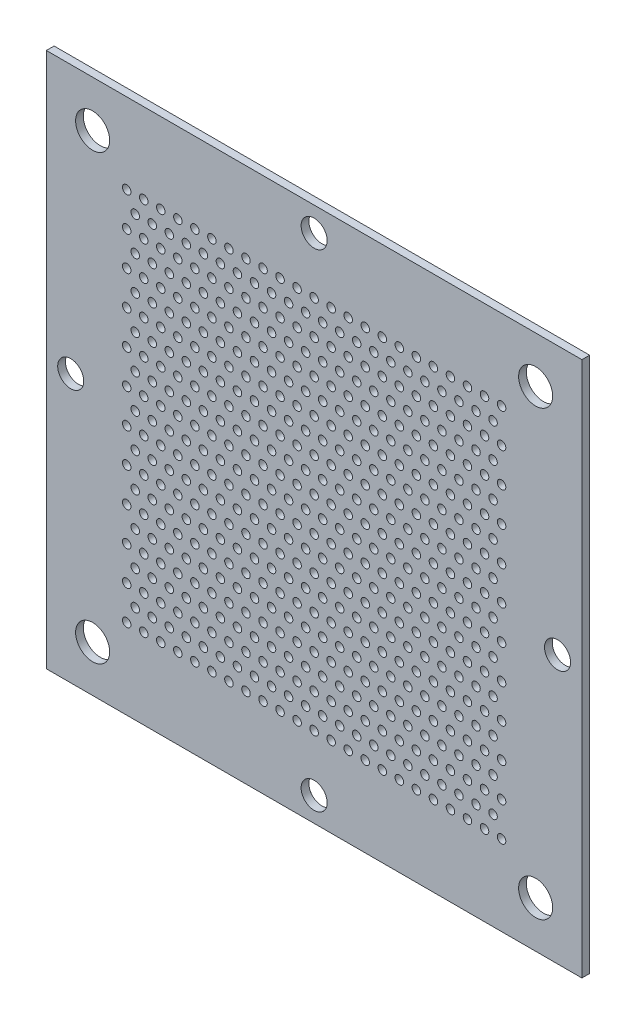
SolidWorks part; units mm, degrees
ref_plane "Front Plane" through (0, 0, 0) normal (0, 0, 1) x (1, 0, 0)
ref_plane "Top Plane" through (0, 0, 0) normal (0, 1, 0) x (1, 0, 0)
ref_plane "Right Plane" through (0, 0, 0) normal (1, 0, 0) x (0, 0, -1)
sketch "Model" plane through (0, 0, 0) normal (0, 0, 1) x (1, 0, 0)
  line L0 (-16.5, -16.5) -> (-16.5, 93.5)
  line L1 (-16.5, 93.5) -> (93.5, 93.5)
  line L2 (93.5, 93.5) -> (93.5, -16.5)
  line L3 (93.5, -16.5) -> (-16.5, -16.5)
  circle A0 centre (84, 84) radius 3.5
  circle A1 centre (-7, 84) radius 3.5
  circle A2 centre (-7, -7) radius 3.5
  circle A3 centre (84, -7) radius 3.5
  circle A4 centre (77, 0) radius 0.875
  circle A5 centre (73.5, 0) radius 0.875
  circle A6 centre (70, 0) radius 0.875
  circle A7 centre (66.5, 0) radius 0.875
  circle A8 centre (63, 0) radius 0.875
  circle A9 centre (59.5, 0) radius 0.875
  circle A10 centre (56, 0) radius 0.875
  circle A11 centre (52.5, 0) radius 0.875
  circle A12 centre (49, 0) radius 0.875
  circle A13 centre (45.5, 0) radius 0.875
  circle A14 centre (42, 0) radius 0.875
  circle A15 centre (38.5, 0) radius 0.875
  circle A16 centre (35, 0) radius 0.875
  circle A17 centre (31.5, 0) radius 0.875
  circle A18 centre (28, 0) radius 0.875
  circle A19 centre (24.5, 0) radius 0.875
  circle A20 centre (21, 0) radius 0.875
  circle A21 centre (17.5, 0) radius 0.875
  circle A22 centre (14, 0) radius 0.875
  circle A23 centre (10.5, 0) radius 0.875
  circle A24 centre (7, 0) radius 0.875
  circle A25 centre (3.5, 0) radius 0.875
  circle A26 centre (0, 0) radius 0.875
  circle A27 centre (75.25, 3.5) radius 0.875
  circle A28 centre (71.75, 3.5) radius 0.875
  circle A29 centre (68.25, 3.5) radius 0.875
  circle A30 centre (64.75, 3.5) radius 0.875
  circle A31 centre (61.25, 3.5) radius 0.875
  circle A32 centre (57.75, 3.5) radius 0.875
  circle A33 centre (54.25, 3.5) radius 0.875
  circle A34 centre (50.75, 3.5) radius 0.875
  circle A35 centre (47.25, 3.5) radius 0.875
  circle A36 centre (43.75, 3.5) radius 0.875
  circle A37 centre (40.25, 3.5) radius 0.875
  circle A38 centre (36.75, 3.5) radius 0.875
  circle A39 centre (33.25, 3.5) radius 0.875
  circle A40 centre (29.75, 3.5) radius 0.875
  circle A41 centre (26.25, 3.5) radius 0.875
  circle A42 centre (22.75, 3.5) radius 0.875
  circle A43 centre (19.25, 3.5) radius 0.875
  circle A44 centre (15.75, 3.5) radius 0.875
  circle A45 centre (12.25, 3.5) radius 0.875
  circle A46 centre (8.75, 3.5) radius 0.875
  circle A47 centre (5.25, 3.5) radius 0.875
  circle A48 centre (1.75, 3.5) radius 0.875
  circle A49 centre (77, 7) radius 0.875
  circle A50 centre (73.5, 7) radius 0.875
  circle A51 centre (70, 7) radius 0.875
  circle A52 centre (66.5, 7) radius 0.875
  circle A53 centre (63, 7) radius 0.875
  circle A54 centre (59.5, 7) radius 0.875
  circle A55 centre (56, 7) radius 0.875
  circle A56 centre (52.5, 7) radius 0.875
  circle A57 centre (49, 7) radius 0.875
  circle A58 centre (45.5, 7) radius 0.875
  circle A59 centre (42, 7) radius 0.875
  circle A60 centre (38.5, 7) radius 0.875
  circle A61 centre (35, 7) radius 0.875
  circle A62 centre (31.5, 7) radius 0.875
  circle A63 centre (28, 7) radius 0.875
  circle A64 centre (24.5, 7) radius 0.875
  circle A65 centre (21, 7) radius 0.875
  circle A66 centre (17.5, 7) radius 0.875
  circle A67 centre (14, 7) radius 0.875
  circle A68 centre (10.5, 7) radius 0.875
  circle A69 centre (7, 7) radius 0.875
  circle A70 centre (3.5, 7) radius 0.875
  circle A71 centre (0, 7) radius 0.875
  circle A72 centre (75.25, 10.5) radius 0.875
  circle A73 centre (71.75, 10.5) radius 0.875
  circle A74 centre (68.25, 10.5) radius 0.875
  circle A75 centre (64.75, 10.5) radius 0.875
  circle A76 centre (61.25, 10.5) radius 0.875
  circle A77 centre (57.75, 10.5) radius 0.875
  circle A78 centre (54.25, 10.5) radius 0.875
  circle A79 centre (50.75, 10.5) radius 0.875
  circle A80 centre (47.25, 10.5) radius 0.875
  circle A81 centre (43.75, 10.5) radius 0.875
  circle A82 centre (40.25, 10.5) radius 0.875
  circle A83 centre (36.75, 10.5) radius 0.875
  circle A84 centre (33.25, 10.5) radius 0.875
  circle A85 centre (29.75, 10.5) radius 0.875
  circle A86 centre (26.25, 10.5) radius 0.875
  circle A87 centre (22.75, 10.5) radius 0.875
  circle A88 centre (19.25, 10.5) radius 0.875
  circle A89 centre (15.75, 10.5) radius 0.875
  circle A90 centre (12.25, 10.5) radius 0.875
  circle A91 centre (8.75, 10.5) radius 0.875
  circle A92 centre (5.25, 10.5) radius 0.875
  circle A93 centre (1.75, 10.5) radius 0.875
  circle A94 centre (77, 14) radius 0.875
  circle A95 centre (73.5, 14) radius 0.875
  circle A96 centre (70, 14) radius 0.875
  circle A97 centre (66.5, 14) radius 0.875
  circle A98 centre (63, 14) radius 0.875
  circle A99 centre (59.5, 14) radius 0.875
  circle A100 centre (56, 14) radius 0.875
  circle A101 centre (52.5, 14) radius 0.875
  circle A102 centre (49, 14) radius 0.875
  circle A103 centre (45.5, 14) radius 0.875
  circle A104 centre (42, 14) radius 0.875
  circle A105 centre (38.5, 14) radius 0.875
  circle A106 centre (35, 14) radius 0.875
  circle A107 centre (31.5, 14) radius 0.875
  circle A108 centre (28, 14) radius 0.875
  circle A109 centre (24.5, 14) radius 0.875
  circle A110 centre (21, 14) radius 0.875
  circle A111 centre (17.5, 14) radius 0.875
  circle A112 centre (14, 14) radius 0.875
  circle A113 centre (10.5, 14) radius 0.875
  circle A114 centre (7, 14) radius 0.875
  circle A115 centre (3.5, 14) radius 0.875
  circle A116 centre (0, 14) radius 0.875
  circle A117 centre (75.25, 17.5) radius 0.875
  circle A118 centre (71.75, 17.5) radius 0.875
  circle A119 centre (68.25, 17.5) radius 0.875
  circle A120 centre (64.75, 17.5) radius 0.875
  circle A121 centre (61.25, 17.5) radius 0.875
  circle A122 centre (57.75, 17.5) radius 0.875
  circle A123 centre (54.25, 17.5) radius 0.875
  circle A124 centre (50.75, 17.5) radius 0.875
  circle A125 centre (47.25, 17.5) radius 0.875
  circle A126 centre (43.75, 17.5) radius 0.875
  circle A127 centre (40.25, 17.5) radius 0.875
  circle A128 centre (36.75, 17.5) radius 0.875
  circle A129 centre (33.25, 17.5) radius 0.875
  circle A130 centre (29.75, 17.5) radius 0.875
  circle A131 centre (26.25, 17.5) radius 0.875
  circle A132 centre (22.75, 17.5) radius 0.875
  circle A133 centre (19.25, 17.5) radius 0.875
  circle A134 centre (15.75, 17.5) radius 0.875
  circle A135 centre (12.25, 17.5) radius 0.875
  circle A136 centre (8.75, 17.5) radius 0.875
  circle A137 centre (5.25, 17.5) radius 0.875
  circle A138 centre (1.75, 17.5) radius 0.875
  circle A139 centre (77, 21) radius 0.875
  circle A140 centre (73.5, 21) radius 0.875
  circle A141 centre (70, 21) radius 0.875
  circle A142 centre (66.5, 21) radius 0.875
  circle A143 centre (63, 21) radius 0.875
  circle A144 centre (59.5, 21) radius 0.875
  circle A145 centre (56, 21) radius 0.875
  circle A146 centre (52.5, 21) radius 0.875
  circle A147 centre (49, 21) radius 0.875
  circle A148 centre (45.5, 21) radius 0.875
  circle A149 centre (42, 21) radius 0.875
  circle A150 centre (38.5, 21) radius 0.875
  circle A151 centre (35, 21) radius 0.875
  circle A152 centre (31.5, 21) radius 0.875
  circle A153 centre (28, 21) radius 0.875
  circle A154 centre (24.5, 21) radius 0.875
  circle A155 centre (21, 21) radius 0.875
  circle A156 centre (17.5, 21) radius 0.875
  circle A157 centre (14, 21) radius 0.875
  circle A158 centre (10.5, 21) radius 0.875
  circle A159 centre (7, 21) radius 0.875
  circle A160 centre (3.5, 21) radius 0.875
  circle A161 centre (0, 21) radius 0.875
  circle A162 centre (75.25, 24.5) radius 0.875
  circle A163 centre (71.75, 24.5) radius 0.875
  circle A164 centre (68.25, 24.5) radius 0.875
  circle A165 centre (64.75, 24.5) radius 0.875
  circle A166 centre (61.25, 24.5) radius 0.875
  circle A167 centre (57.75, 24.5) radius 0.875
  circle A168 centre (54.25, 24.5) radius 0.875
  circle A169 centre (50.75, 24.5) radius 0.875
  circle A170 centre (47.25, 24.5) radius 0.875
  circle A171 centre (43.75, 24.5) radius 0.875
  circle A172 centre (40.25, 24.5) radius 0.875
  circle A173 centre (36.75, 24.5) radius 0.875
  circle A174 centre (33.25, 24.5) radius 0.875
  circle A175 centre (29.75, 24.5) radius 0.875
  circle A176 centre (26.25, 24.5) radius 0.875
  circle A177 centre (22.75, 24.5) radius 0.875
  circle A178 centre (19.25, 24.5) radius 0.875
  circle A179 centre (15.75, 24.5) radius 0.875
  circle A180 centre (12.25, 24.5) radius 0.875
  circle A181 centre (8.75, 24.5) radius 0.875
  circle A182 centre (5.25, 24.5) radius 0.875
  circle A183 centre (1.75, 24.5) radius 0.875
  circle A184 centre (77, 28) radius 0.875
  circle A185 centre (73.5, 28) radius 0.875
  circle A186 centre (70, 28) radius 0.875
  circle A187 centre (66.5, 28) radius 0.875
  circle A188 centre (63, 28) radius 0.875
  circle A189 centre (59.5, 28) radius 0.875
  circle A190 centre (56, 28) radius 0.875
  circle A191 centre (52.5, 28) radius 0.875
  circle A192 centre (49, 28) radius 0.875
  circle A193 centre (45.5, 28) radius 0.875
  circle A194 centre (42, 28) radius 0.875
  circle A195 centre (38.5, 28) radius 0.875
  circle A196 centre (35, 28) radius 0.875
  circle A197 centre (31.5, 28) radius 0.875
  circle A198 centre (28, 28) radius 0.875
  circle A199 centre (24.5, 28) radius 0.875
  circle A200 centre (21, 28) radius 0.875
  circle A201 centre (17.5, 28) radius 0.875
  circle A202 centre (14, 28) radius 0.875
  circle A203 centre (10.5, 28) radius 0.875
  circle A204 centre (7, 28) radius 0.875
  circle A205 centre (3.5, 28) radius 0.875
  circle A206 centre (0, 28) radius 0.875
  circle A207 centre (75.25, 31.5) radius 0.875
  circle A208 centre (71.75, 31.5) radius 0.875
  circle A209 centre (68.25, 31.5) radius 0.875
  circle A210 centre (64.75, 31.5) radius 0.875
  circle A211 centre (61.25, 31.5) radius 0.875
  circle A212 centre (57.75, 31.5) radius 0.875
  circle A213 centre (54.25, 31.5) radius 0.875
  circle A214 centre (50.75, 31.5) radius 0.875
  circle A215 centre (47.25, 31.5) radius 0.875
  circle A216 centre (43.75, 31.5) radius 0.875
  circle A217 centre (40.25, 31.5) radius 0.875
  circle A218 centre (36.75, 31.5) radius 0.875
  circle A219 centre (33.25, 31.5) radius 0.875
  circle A220 centre (29.75, 31.5) radius 0.875
  circle A221 centre (26.25, 31.5) radius 0.875
  circle A222 centre (22.75, 31.5) radius 0.875
  circle A223 centre (19.25, 31.5) radius 0.875
  circle A224 centre (15.75, 31.5) radius 0.875
  circle A225 centre (12.25, 31.5) radius 0.875
  circle A226 centre (8.75, 31.5) radius 0.875
  circle A227 centre (5.25, 31.5) radius 0.875
  circle A228 centre (1.75, 31.5) radius 0.875
  circle A229 centre (77, 35) radius 0.875
  circle A230 centre (73.5, 35) radius 0.875
  circle A231 centre (70, 35) radius 0.875
  circle A232 centre (66.5, 35) radius 0.875
  circle A233 centre (63, 35) radius 0.875
  circle A234 centre (59.5, 35) radius 0.875
  circle A235 centre (56, 35) radius 0.875
  circle A236 centre (52.5, 35) radius 0.875
  circle A237 centre (49, 35) radius 0.875
  circle A238 centre (45.5, 35) radius 0.875
  circle A239 centre (42, 35) radius 0.875
  circle A240 centre (38.5, 35) radius 0.875
  circle A241 centre (35, 35) radius 0.875
  circle A242 centre (31.5, 35) radius 0.875
  circle A243 centre (28, 35) radius 0.875
  circle A244 centre (24.5, 35) radius 0.875
  circle A245 centre (21, 35) radius 0.875
  circle A246 centre (17.5, 35) radius 0.875
  circle A247 centre (14, 35) radius 0.875
  circle A248 centre (10.5, 35) radius 0.875
  circle A249 centre (7, 35) radius 0.875
  circle A250 centre (3.5, 35) radius 0.875
  circle A251 centre (0, 35) radius 0.875
  circle A252 centre (75.25, 38.5) radius 0.875
  circle A253 centre (71.75, 38.5) radius 0.875
  circle A254 centre (68.25, 38.5) radius 0.875
  circle A255 centre (64.75, 38.5) radius 0.875
  circle A256 centre (61.25, 38.5) radius 0.875
  circle A257 centre (57.75, 38.5) radius 0.875
  circle A258 centre (54.25, 38.5) radius 0.875
  circle A259 centre (50.75, 38.5) radius 0.875
  circle A260 centre (47.25, 38.5) radius 0.875
  circle A261 centre (43.75, 38.5) radius 0.875
  circle A262 centre (40.25, 38.5) radius 0.875
  circle A263 centre (36.75, 38.5) radius 0.875
  circle A264 centre (33.25, 38.5) radius 0.875
  circle A265 centre (29.75, 38.5) radius 0.875
  circle A266 centre (26.25, 38.5) radius 0.875
  circle A267 centre (22.75, 38.5) radius 0.875
  circle A268 centre (19.25, 38.5) radius 0.875
  circle A269 centre (15.75, 38.5) radius 0.875
  circle A270 centre (12.25, 38.5) radius 0.875
  circle A271 centre (8.75, 38.5) radius 0.875
  circle A272 centre (5.25, 38.5) radius 0.875
  circle A273 centre (1.75, 38.5) radius 0.875
  circle A274 centre (77, 42) radius 0.875
  circle A275 centre (73.5, 42) radius 0.875
  circle A276 centre (70, 42) radius 0.875
  circle A277 centre (66.5, 42) radius 0.875
  circle A278 centre (63, 42) radius 0.875
  circle A279 centre (59.5, 42) radius 0.875
  circle A280 centre (56, 42) radius 0.875
  circle A281 centre (52.5, 42) radius 0.875
  circle A282 centre (49, 42) radius 0.875
  circle A283 centre (45.5, 42) radius 0.875
  circle A284 centre (42, 42) radius 0.875
  circle A285 centre (38.5, 42) radius 0.875
  circle A286 centre (35, 42) radius 0.875
  circle A287 centre (31.5, 42) radius 0.875
  circle A288 centre (28, 42) radius 0.875
  circle A289 centre (24.5, 42) radius 0.875
  circle A290 centre (21, 42) radius 0.875
  circle A291 centre (17.5, 42) radius 0.875
  circle A292 centre (14, 42) radius 0.875
  circle A293 centre (10.5, 42) radius 0.875
  circle A294 centre (7, 42) radius 0.875
  circle A295 centre (3.5, 42) radius 0.875
  circle A296 centre (0, 42) radius 0.875
  circle A297 centre (75.25, 45.5) radius 0.875
  circle A298 centre (71.75, 45.5) radius 0.875
  circle A299 centre (68.25, 45.5) radius 0.875
  circle A300 centre (64.75, 45.5) radius 0.875
  circle A301 centre (61.25, 45.5) radius 0.875
  circle A302 centre (57.75, 45.5) radius 0.875
  circle A303 centre (54.25, 45.5) radius 0.875
  circle A304 centre (50.75, 45.5) radius 0.875
  circle A305 centre (47.25, 45.5) radius 0.875
  circle A306 centre (43.75, 45.5) radius 0.875
  circle A307 centre (40.25, 45.5) radius 0.875
  circle A308 centre (36.75, 45.5) radius 0.875
  circle A309 centre (33.25, 45.5) radius 0.875
  circle A310 centre (29.75, 45.5) radius 0.875
  circle A311 centre (26.25, 45.5) radius 0.875
  circle A312 centre (22.75, 45.5) radius 0.875
  circle A313 centre (19.25, 45.5) radius 0.875
  circle A314 centre (15.75, 45.5) radius 0.875
  circle A315 centre (12.25, 45.5) radius 0.875
  circle A316 centre (8.75, 45.5) radius 0.875
  circle A317 centre (5.25, 45.5) radius 0.875
  circle A318 centre (1.75, 45.5) radius 0.875
  circle A319 centre (77, 49) radius 0.875
  circle A320 centre (73.5, 49) radius 0.875
  circle A321 centre (70, 49) radius 0.875
  circle A322 centre (66.5, 49) radius 0.875
  circle A323 centre (63, 49) radius 0.875
  circle A324 centre (59.5, 49) radius 0.875
  circle A325 centre (56, 49) radius 0.875
  circle A326 centre (52.5, 49) radius 0.875
  circle A327 centre (49, 49) radius 0.875
  circle A328 centre (45.5, 49) radius 0.875
  circle A329 centre (42, 49) radius 0.875
  circle A330 centre (38.5, 49) radius 0.875
  circle A331 centre (35, 49) radius 0.875
  circle A332 centre (31.5, 49) radius 0.875
  circle A333 centre (28, 49) radius 0.875
  circle A334 centre (24.5, 49) radius 0.875
  circle A335 centre (21, 49) radius 0.875
  circle A336 centre (17.5, 49) radius 0.875
  circle A337 centre (14, 49) radius 0.875
  circle A338 centre (10.5, 49) radius 0.875
  circle A339 centre (7, 49) radius 0.875
  circle A340 centre (3.5, 49) radius 0.875
  circle A341 centre (0, 49) radius 0.875
  circle A342 centre (75.25, 52.5) radius 0.875
  circle A343 centre (71.75, 52.5) radius 0.875
  circle A344 centre (68.25, 52.5) radius 0.875
  circle A345 centre (64.75, 52.5) radius 0.875
  circle A346 centre (61.25, 52.5) radius 0.875
  circle A347 centre (57.75, 52.5) radius 0.875
  circle A348 centre (54.25, 52.5) radius 0.875
  circle A349 centre (50.75, 52.5) radius 0.875
  circle A350 centre (47.25, 52.5) radius 0.875
  circle A351 centre (43.75, 52.5) radius 0.875
  circle A352 centre (40.25, 52.5) radius 0.875
  circle A353 centre (36.75, 52.5) radius 0.875
  circle A354 centre (33.25, 52.5) radius 0.875
  circle A355 centre (29.75, 52.5) radius 0.875
  circle A356 centre (26.25, 52.5) radius 0.875
  circle A357 centre (22.75, 52.5) radius 0.875
  circle A358 centre (19.25, 52.5) radius 0.875
  circle A359 centre (15.75, 52.5) radius 0.875
  circle A360 centre (12.25, 52.5) radius 0.875
  circle A361 centre (8.75, 52.5) radius 0.875
  circle A362 centre (5.25, 52.5) radius 0.875
  circle A363 centre (1.75, 52.5) radius 0.875
  circle A364 centre (77, 56) radius 0.875
  circle A365 centre (73.5, 56) radius 0.875
  circle A366 centre (70, 56) radius 0.875
  circle A367 centre (66.5, 56) radius 0.875
  circle A368 centre (63, 56) radius 0.875
  circle A369 centre (59.5, 56) radius 0.875
  circle A370 centre (56, 56) radius 0.875
  circle A371 centre (52.5, 56) radius 0.875
  circle A372 centre (49, 56) radius 0.875
  circle A373 centre (45.5, 56) radius 0.875
  circle A374 centre (42, 56) radius 0.875
  circle A375 centre (38.5, 56) radius 0.875
  circle A376 centre (35, 56) radius 0.875
  circle A377 centre (31.5, 56) radius 0.875
  circle A378 centre (28, 56) radius 0.875
  circle A379 centre (24.5, 56) radius 0.875
  circle A380 centre (21, 56) radius 0.875
  circle A381 centre (17.5, 56) radius 0.875
  circle A382 centre (14, 56) radius 0.875
  circle A383 centre (10.5, 56) radius 0.875
  circle A384 centre (7, 56) radius 0.875
  circle A385 centre (3.5, 56) radius 0.875
  circle A386 centre (0, 56) radius 0.875
  circle A387 centre (75.25, 59.5) radius 0.875
  circle A388 centre (71.75, 59.5) radius 0.875
  circle A389 centre (68.25, 59.5) radius 0.875
  circle A390 centre (64.75, 59.5) radius 0.875
  circle A391 centre (61.25, 59.5) radius 0.875
  circle A392 centre (57.75, 59.5) radius 0.875
  circle A393 centre (54.25, 59.5) radius 0.875
  circle A394 centre (50.75, 59.5) radius 0.875
  circle A395 centre (47.25, 59.5) radius 0.875
  circle A396 centre (43.75, 59.5) radius 0.875
  circle A397 centre (40.25, 59.5) radius 0.875
  circle A398 centre (36.75, 59.5) radius 0.875
  circle A399 centre (33.25, 59.5) radius 0.875
  circle A400 centre (29.75, 59.5) radius 0.875
  circle A401 centre (26.25, 59.5) radius 0.875
  circle A402 centre (22.75, 59.5) radius 0.875
  circle A403 centre (19.25, 59.5) radius 0.875
  circle A404 centre (15.75, 59.5) radius 0.875
  circle A405 centre (12.25, 59.5) radius 0.875
  circle A406 centre (8.75, 59.5) radius 0.875
  circle A407 centre (5.25, 59.5) radius 0.875
  circle A408 centre (1.75, 59.5) radius 0.875
  circle A409 centre (77, 63) radius 0.875
  circle A410 centre (73.5, 63) radius 0.875
  circle A411 centre (70, 63) radius 0.875
  circle A412 centre (66.5, 63) radius 0.875
  circle A413 centre (63, 63) radius 0.875
  circle A414 centre (59.5, 63) radius 0.875
  circle A415 centre (56, 63) radius 0.875
  circle A416 centre (52.5, 63) radius 0.875
  circle A417 centre (49, 63) radius 0.875
  circle A418 centre (45.5, 63) radius 0.875
  circle A419 centre (42, 63) radius 0.875
  circle A420 centre (38.5, 63) radius 0.875
  circle A421 centre (35, 63) radius 0.875
  circle A422 centre (31.5, 63) radius 0.875
  circle A423 centre (28, 63) radius 0.875
  circle A424 centre (24.5, 63) radius 0.875
  circle A425 centre (21, 63) radius 0.875
  circle A426 centre (17.5, 63) radius 0.875
  circle A427 centre (14, 63) radius 0.875
  circle A428 centre (10.5, 63) radius 0.875
  circle A429 centre (7, 63) radius 0.875
  circle A430 centre (3.5, 63) radius 0.875
  circle A431 centre (0, 63) radius 0.875
  circle A432 centre (75.25, 66.5) radius 0.875
  circle A433 centre (71.75, 66.5) radius 0.875
  circle A434 centre (68.25, 66.5) radius 0.875
  circle A435 centre (64.75, 66.5) radius 0.875
  circle A436 centre (61.25, 66.5) radius 0.875
  circle A437 centre (57.75, 66.5) radius 0.875
  circle A438 centre (54.25, 66.5) radius 0.875
  circle A439 centre (50.75, 66.5) radius 0.875
  circle A440 centre (47.25, 66.5) radius 0.875
  circle A441 centre (43.75, 66.5) radius 0.875
  circle A442 centre (40.25, 66.5) radius 0.875
  circle A443 centre (36.75, 66.5) radius 0.875
  circle A444 centre (33.25, 66.5) radius 0.875
  circle A445 centre (29.75, 66.5) radius 0.875
  circle A446 centre (26.25, 66.5) radius 0.875
  circle A447 centre (22.75, 66.5) radius 0.875
  circle A448 centre (19.25, 66.5) radius 0.875
  circle A449 centre (15.75, 66.5) radius 0.875
  circle A450 centre (12.25, 66.5) radius 0.875
  circle A451 centre (8.75, 66.5) radius 0.875
  circle A452 centre (5.25, 66.5) radius 0.875
  circle A453 centre (1.75, 66.5) radius 0.875
  circle A454 centre (77, 70) radius 0.875
  circle A455 centre (73.5, 70) radius 0.875
  circle A456 centre (70, 70) radius 0.875
  circle A457 centre (66.5, 70) radius 0.875
  circle A458 centre (63, 70) radius 0.875
  circle A459 centre (59.5, 70) radius 0.875
  circle A460 centre (56, 70) radius 0.875
  circle A461 centre (52.5, 70) radius 0.875
  circle A462 centre (49, 70) radius 0.875
  circle A463 centre (45.5, 70) radius 0.875
  circle A464 centre (42, 70) radius 0.875
  circle A465 centre (38.5, 70) radius 0.875
  circle A466 centre (35, 70) radius 0.875
  circle A467 centre (31.5, 70) radius 0.875
  circle A468 centre (28, 70) radius 0.875
  circle A469 centre (24.5, 70) radius 0.875
  circle A470 centre (21, 70) radius 0.875
  circle A471 centre (17.5, 70) radius 0.875
  circle A472 centre (14, 70) radius 0.875
  circle A473 centre (10.5, 70) radius 0.875
  circle A474 centre (7, 70) radius 0.875
  circle A475 centre (3.5, 70) radius 0.875
  circle A476 centre (0, 70) radius 0.875
  circle A477 centre (75.25, 73.5) radius 0.875
  circle A478 centre (71.75, 73.5) radius 0.875
  circle A479 centre (68.25, 73.5) radius 0.875
  circle A480 centre (64.75, 73.5) radius 0.875
  circle A481 centre (61.25, 73.5) radius 0.875
  circle A482 centre (57.75, 73.5) radius 0.875
  circle A483 centre (54.25, 73.5) radius 0.875
  circle A484 centre (50.75, 73.5) radius 0.875
  circle A485 centre (47.25, 73.5) radius 0.875
  circle A486 centre (43.75, 73.5) radius 0.875
  circle A487 centre (40.25, 73.5) radius 0.875
  circle A488 centre (36.75, 73.5) radius 0.875
  circle A489 centre (33.25, 73.5) radius 0.875
  circle A490 centre (29.75, 73.5) radius 0.875
  circle A491 centre (26.25, 73.5) radius 0.875
  circle A492 centre (22.75, 73.5) radius 0.875
  circle A493 centre (19.25, 73.5) radius 0.875
  circle A494 centre (15.75, 73.5) radius 0.875
  circle A495 centre (12.25, 73.5) radius 0.875
  circle A496 centre (8.75, 73.5) radius 0.875
  circle A497 centre (5.25, 73.5) radius 0.875
  circle A498 centre (1.75, 73.5) radius 0.875
  circle A499 centre (77, 77) radius 0.875
  circle A500 centre (73.5, 77) radius 0.875
  circle A501 centre (70, 77) radius 0.875
  circle A502 centre (66.5, 77) radius 0.875
  circle A503 centre (63, 77) radius 0.875
  circle A504 centre (59.5, 77) radius 0.875
  circle A505 centre (56, 77) radius 0.875
  circle A506 centre (52.5, 77) radius 0.875
  circle A507 centre (49, 77) radius 0.875
  circle A508 centre (45.5, 77) radius 0.875
  circle A509 centre (42, 77) radius 0.875
  circle A510 centre (38.5, 77) radius 0.875
  circle A511 centre (35, 77) radius 0.875
  circle A512 centre (31.5, 77) radius 0.875
  circle A513 centre (28, 77) radius 0.875
  circle A514 centre (24.5, 77) radius 0.875
  circle A515 centre (21, 77) radius 0.875
  circle A516 centre (17.5, 77) radius 0.875
  circle A517 centre (14, 77) radius 0.875
  circle A518 centre (10.5, 77) radius 0.875
  circle A519 centre (7, 77) radius 0.875
  circle A520 centre (3.5, 77) radius 0.875
  circle A521 centre (0, 77) radius 0.875
  circle A522 centre (-11.5, 38.5) radius 2.675
  circle A523 centre (38.5, -11.5) radius 2.675
  circle A524 centre (88.5, 38.5) radius 2.675
  circle A525 centre (38.5, 88.5) radius 2.675
extrude "Boss-Extrude1" add sketch "Model" along normal blind 1.5875
